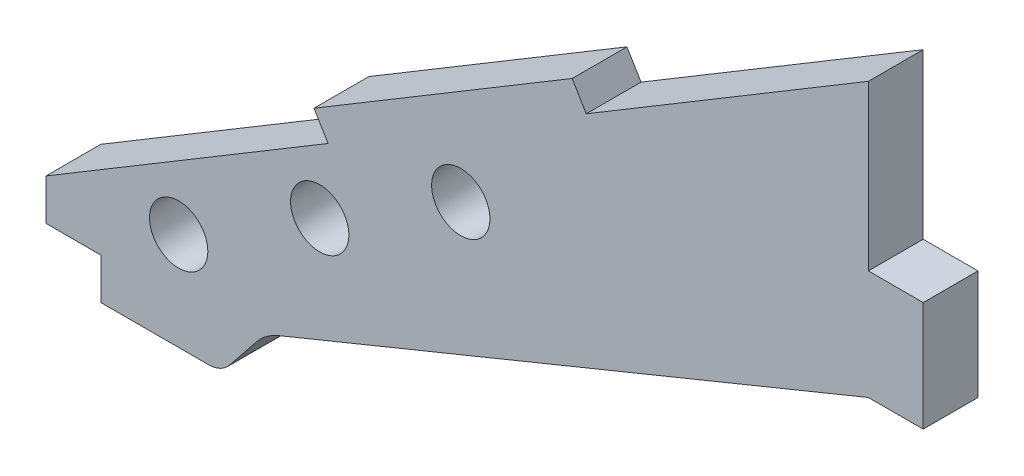
SolidWorks part; units mm, degrees
material "Plain Carbon Steel"
ref_plane "Front Plane" through (0, 0, 0) normal (0, 0, 1) x (1, 0, 0)
ref_plane "Top Plane" through (0, 0, 0) normal (0, 1, 0) x (1, 0, 0)
ref_plane "Right Plane" through (0, 0, 0) normal (1, 0, 0) x (0, 0, -1)
sketch "Sketch1" plane through (0, 0, 0) normal (0, 0, 1) x (1, 0, 0)
  line L0 (0, 57.1189) -> (0, 0)
  line L1 (0, 0) -> (-95.25, 0)
  line L2 (-95.25, 0) -> (0, 57.1189)
  line L3 (-88.9, 0) -> (-88.9, -19.05)
  line L4 (-88.9, -19.05) -> (-82.55, -19.05)
  line L5 (-82.55, -19.05) -> (0, 0)
  dimension "D1" = 30.95
  dimension "D2" = 95.25
  dimension "D3" = 6.35
  dimension "D4" = 19.05
  dimension "D5" = 6.35
extrude "Boss-Extrude1" add sketch "Sketch1" along normal blind 6.35 contours L4 L5 L1 L3 | L2 L1 L0
sketch "Sketch3" plane through (0, 0, 6.35) normal (0, 0, 1) x (1, 0, 0)
  line L0 (-82.55, -19.05) -> (-69.85, -3.175)
  line L2 (0, 0) -> (-82.55, -19.05)
  line L3 (-69.85, -3.175) -> (0, 25.4)
  line L4 (0, 57.1189) -> (0, 0) construction
  line L5 (0, 25.4) -> (0, 0)
  dimension "D1" = 15.875
  dimension "D2" = 12.7
  dimension "D3" = 25.4
extrude "Cut-Extrude2" cut sketch "Sketch3" against normal through all
fillet "Fillet2" radius 6.35 1 edges at (-69.85, -3.175, 3.175)
sketch "Sketch4" plane through (0, 0, 6.35) normal (0, 0, 1) x (1, 0, 0)
  line L0 (-88.9, 0) -> (-88.9, -19.05) construction
  line L1 (0, 25.4) -> (6.35, 25.4)
  line L2 (0, 25.4) -> (0, 38.1)
  line L3 (0, 38.1) -> (6.35, 38.1)
  line L4 (6.35, 25.4) -> (6.35, 38.1)
  line L5 (-95.25, 0) -> (-88.9, 0)
  line L6 (-95.25, 0) -> (-95.25, -4.7625)
  line L7 (-95.25, -4.7625) -> (-88.9, -4.7625)
  line L8 (-88.9, 0) -> (-88.9, -4.7625)
  dimension "D1" = 6.35
  dimension "D2" = 12.7
  dimension "D3" = 4.7625
extrude "Boss-Extrude2" add sketch "Sketch4" against normal up to surface (6.35 mm away) up to face at (-61.8658, 4.6961, 0)
sketch "Sketch5" plane through (0, 0, 6.35) normal (0, 0, 1) x (1, 0, 0)
  line L0 (-70.8793, -4.4616) -> (-82.55, -19.05) construction
  line L1 (-74.93, -9.525) -> (-88.9, -9.525)
  line L2 (-74.93, -9.525) -> (-74.93, -19.05)
  line L3 (-74.93, -19.05) -> (-88.9, -19.05)
  line L4 (-88.9, -9.525) -> (-88.9, -19.05)
  line L5 (-95.25, -4.7625) -> (-88.9, -4.7625) construction
  dimension "D1" = 4.7625
extrude "Cut-Extrude3" cut sketch "Sketch5" against normal through all
fillet "Fillet3" radius 3.175 1 edges at (-74.93, -9.525, 3.175)
hole_wizard "1/4 Clearance Hole1" positions "Sketch7" profile "Sketch6" hole size "1/4" standard "ANSI Inch" end condition through all
sketch "Sketch7" plane through (0, 0, 6.35) normal (0, 0, 1) x (1, 0, 0)
  line L0 (-87.2342, 4.8068) -> (-80.7028, -6.0849) construction
  line L1 (-95.25, 0) -> (0, 57.1189) construction
  line L2 (-80.7028, -6.0849) -> (-22.225, 28.9827) construction
  line L3 (-22.225, 28.9827) -> (-28.7565, 39.8744) construction
  line L4 (-28.7565, 39.8744) -> (-87.2342, 4.8068) construction
  line L6 (-83.9685, -0.639) -> (-25.4907, 34.4285) construction
  line L8 (0, 57.1189) -> (0, 38.1) construction
  point P19 (-79.8841, 1.8103)
  point P21 (-63.5465, 11.6075)
  point P25 (-47.2089, 21.4047)
  dimension "D1" = 22.225
  dimension "D2" = 12.7
  dimension "D3" = 6.35
  dimension "D4" = 19.05
  dimension "D6" = 19.05
  dimension "D7" = 4.7625
sketch "Sketch6" plane through (-79.8841, 1.8103, 6.35) normal (1, 0, 0) x (0, -1, 0)
  line L0 (0, 0) -> (0, 6.35)
  line L1 (0, 6.35) -> (3.3782, 6.35)
  line L2 (3.3782, 6.35) -> (3.3782, 0)
  line L5 (3.3782, 0) -> (0, 0)
  line L11 (0, -6.35) -> (0, 107.95) construction
  dimension "Thru Hole Dia." = 6.7564
  dimension "Thru Hole Depth" = 6.35
sketch "Sketch8" plane through (0, 0, 6.35) normal (0, 0, 1) x (1, 0, 0)
  line L0 (-32.6752, 37.5245) -> (-34.3081, 40.2474)
  line L1 (-95.25, 0) -> (0, 57.1189) construction
  line L2 (-34.3081, 40.2474) -> (-64.2077, 22.3174)
  line L3 (-64.2077, 22.3174) -> (-62.5748, 19.5944)
  line L4 (-62.5748, 19.5944) -> (-32.6752, 37.5245)
  dimension "D1" = 3.175
  dimension "D2" = 38.1
  dimension "D3" = 38.1
extrude "Boss-Extrude3" add sketch "Sketch8" against normal up to surface (6.35 mm away) up to face at (-76.5059, 1.8103, 0)
